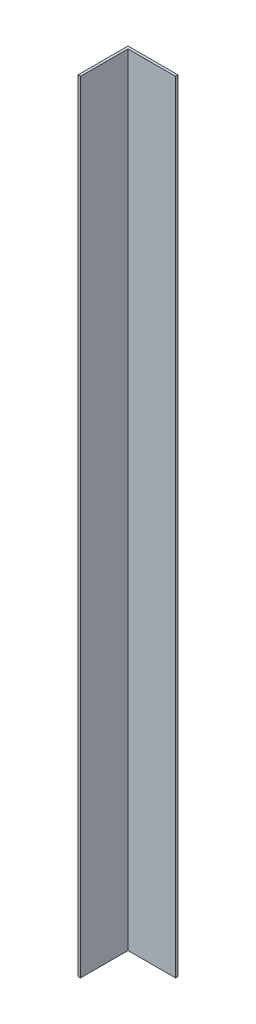
SolidWorks part; units mm, degrees
ref_plane "Plan de face" through (0, 0, 0) normal (0, 0, 1) x (1, 0, 0)
ref_plane "Plan de dessus" through (0, 0, 0) normal (0, 1, 0) x (1, 0, 0)
ref_plane "Plan de droite" through (0, 0, 0) normal (1, 0, 0) x (0, 0, -1)
sketch "Esquisse1" plane through (0, 0, 0) normal (0, 1, 0) x (1, 0, 0)
  line L1 (-20, 20.1136) -> (20, 20.1136)
  line L2 (-20, 20.1136) -> (-20, -19.8864)
  line L3 (-20, -19.8864) -> (-18, -19.8864)
  line L4 (20, 20.1136) -> (20, 18.1136)
  line L5 (-18, 18.1136) -> (20, 18.1136)
  line L6 (-18, 18.1136) -> (-18, -19.8864)
  dimension "D1" = 20
  dimension "D2" = 40
  dimension "D3" = 40
  dimension "D4" = 2
  dimension "D5" = 2
extrude "Boss.-Extru.1" add sketch "Esquisse1" along normal blind 624
